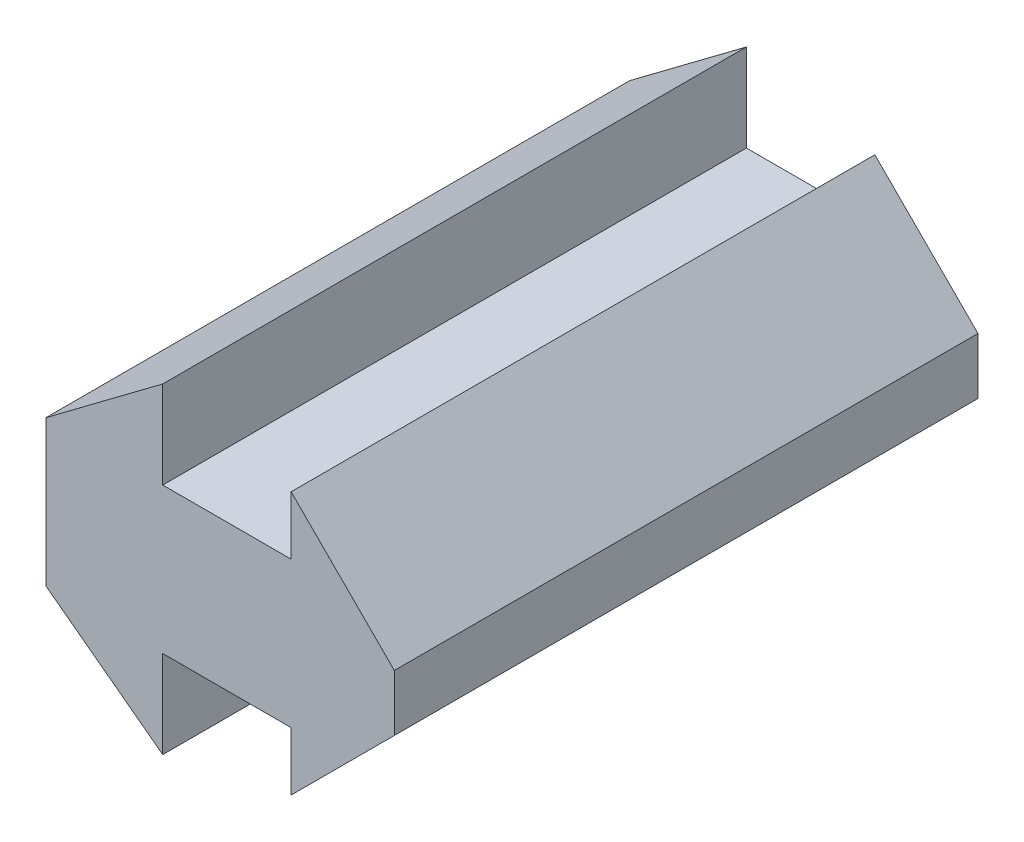
SolidWorks part; units mm, degrees
ref_plane "Plan de face" through (0, 0, 0) normal (0, 0, 1) x (1, 0, 0)
ref_plane "Plan de dessus" through (0, 0, 0) normal (0, 1, 0) x (1, 0, 0)
ref_plane "Plan de droite" through (0, 0, 0) normal (1, 0, 0) x (0, 0, -1)
sketch "ProfileRainureEsquisse" plane through (0, 0, 0) normal (0, 0, 1) x (1, 0, 0)
  line L0 (0, 0) -> (0, 5)
  line L1 (0, 5) -> (4, 8)
  line L2 (0, 0) -> (4, -3)
  line L3 (4, 8) -> (4, 5)
  line L4 (4, 5) -> (8.4, 5)
  line L5 (8.4, 0) -> (8.4, -2)
  line L6 (8.4, 0) -> (4, 0)
  line L7 (4, 0) -> (4, -3)
  line L8 (8.4, 5) -> (8.4, 7)
  line L11 (8.4, 7) -> (11.9355, 3.4645)
  line L12 (11.9355, 3.4645) -> (11.9355, 1.5355)
  line L13 (11.9355, 1.5355) -> (8.4, -2)
  point P4 (0, 2.5)
  point P14 (10.4, 2.5)
  dimension "D1" = 4
  dimension "D2" = 4.4
  dimension "D3" = 5
  dimension "D4" = 8
  dimension "D5" = 45
  dimension "D6" = 2
extrude "Boss.-Extru.1" add sketch "ProfileRainureEsquisse" along normal blind 20
